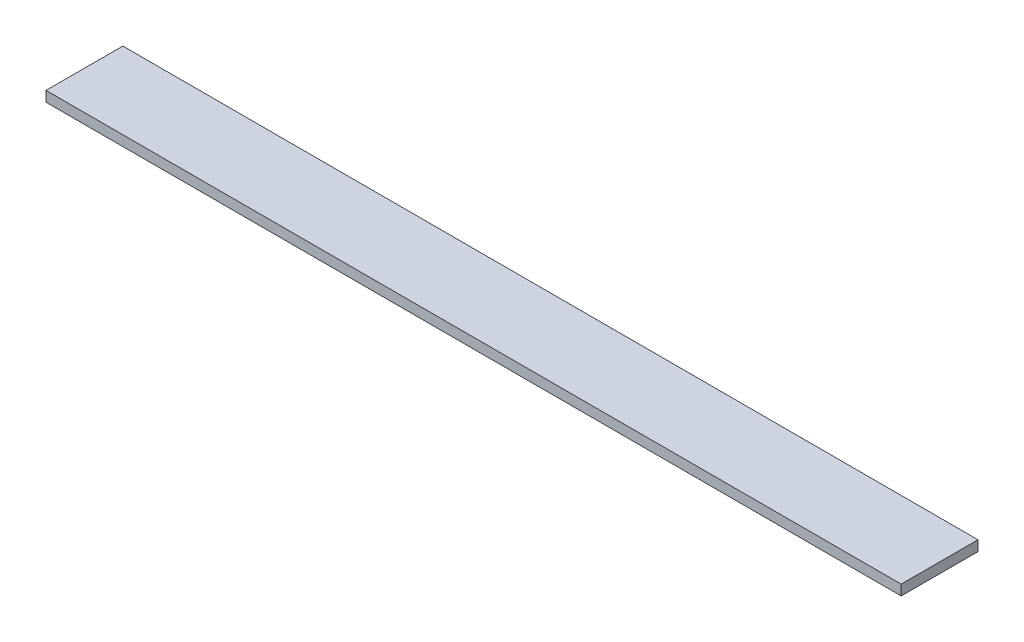
SolidWorks part; units mm, degrees
ref_plane "Спереди" through (0, 0, 0) normal (0, 0, 1) x (1, 0, 0)
ref_plane "Сверху" through (0, 0, 0) normal (0, 1, 0) x (1, 0, 0)
ref_plane "Справа" through (0, 0, 0) normal (1, 0, 0) x (0, 0, -1)
sketch "Эскиз1" plane through (0, 0, 0) normal (1, 0, 0) x (0, 0, -1)
  line L1 (-15, -2) -> (15, -2)
  line L2 (-15, -2) -> (-15, 2)
  line L3 (-15, 2) -> (15, 2)
  line L4 (15, -2) -> (15, 2)
  line L5 (-15, -2) -> (15, 2) construction
  line L6 (-15, 2) -> (15, -2) construction
  point P0 (0, 0)
  dimension "D1" = 4
  dimension "D2" = 30
extrude "Бобышка-Вытянуть1" add sketch "Эскиз1" along normal blind 334
